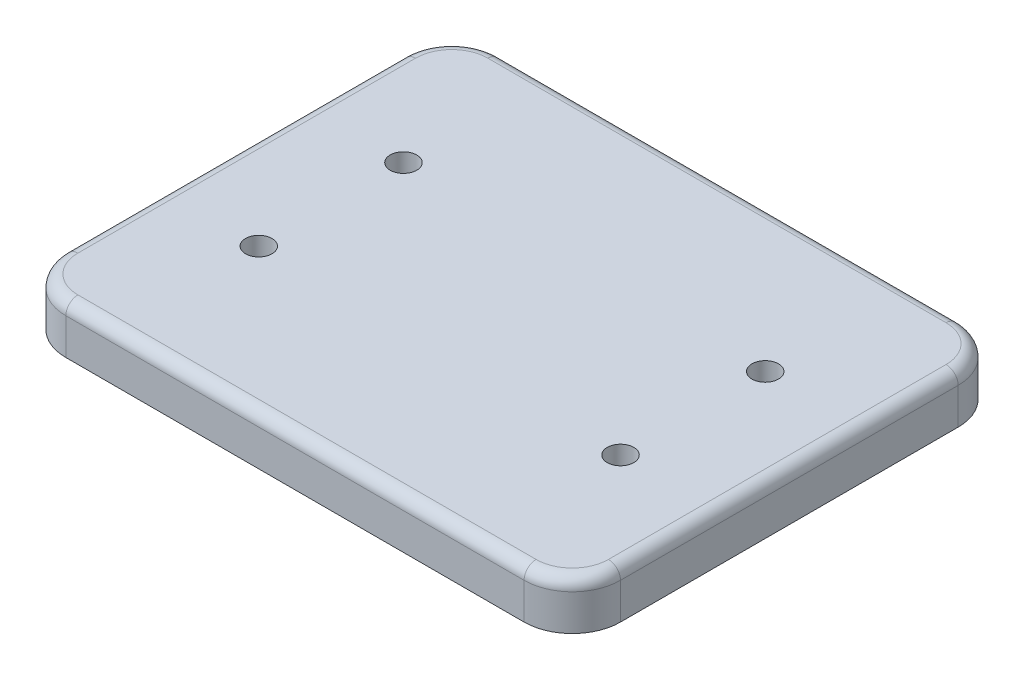
SolidWorks part; units mm, degrees
material "Oak"
ref_plane "Front Plane" through (0, 0, 0) normal (0, 0, 1) x (1, 0, 0)
ref_plane "Top Plane" through (0, 0, 0) normal (0, 1, 0) x (1, 0, 0)
ref_plane "Right Plane" through (0, 0, 0) normal (1, 0, 0) x (0, 0, -1)
sketch "Sketch1" plane through (0, 0, 0) normal (0, 1, 0) x (1, 0, 0)
  line L1 (-115, -90) -> (115, -90)
  line L2 (-115, -90) -> (-115, 90)
  line L3 (-115, 90) -> (115, 90)
  line L4 (115, -90) -> (115, 90)
  line L5 (-115, -90) -> (115, 90) construction
  line L6 (-115, 90) -> (115, -90) construction
  point P0 (0, 0)
  dimension "D1" = 230
  dimension "D2" = 180
extrude "Base" add sketch "Sketch1" along normal blind 20
fillet "R20 Fillets" radius 20 4 edges at (-115, 10, 90) (-115, 10, -90) (115, 10, -90) (115, 10, 90)
fillet "R5 Fillets" radius 5 8 edges at (-109.1421, 20, 84.1421) (-115, 20, 0) (-109.1421, 20, -84.1421) (0, 20, -90) (109.1421, 20, -84.1421) (115, 20, 0) (109.1421, 20, 84.1421) (0, 20, 90)
hole_wizard "Bolt Holes" positions "Sketch15" profile "Sketch10" legacy end condition through all
sketch "Sketch15" plane through (0, 0, 0) normal (0, -1, 0) x (-1, 0, 0)
  line L0 (0, 0) -> (0, 87.5586) construction
  line L2 (0, 0) -> (-115, 0) construction
  line L3 (-115, -70) -> (-115, 70) construction
  point P0 (-75, 30)
  point P2 (-75, -30)
  point P4 (75, -30)
  point P6 (75, 30)
  dimension "D1" = 60
  dimension "D2" = 60
  dimension "D3" = 150
  dimension "D4" = 150
sketch "Sketch10" plane through (75, 0, -30) normal (1, 0, 0) x (0, 0, -1)
  line L0 (0, 0) -> (0, 23.3047)
  line L1 (0, 23.3047) -> (5.5, 20)
  line L2 (5.5, 20) -> (5.5, 11)
  line L3 (5.5, 11) -> (9, 11)
  line L4 (9, 0) -> (0, 0)
  line L5 (0, -11.3109) -> (0, 121.1557) construction
  line L6 (0, 23.3047) -> (-5.5, 20) construction
  line L7 (9, 11) -> (9, 0)
  dimension "Depth" = 20
  dimension "Drill Angle" = 118
  dimension "Diameter" = 11
  dimension "C-Bore Diameter" = 18
  dimension "C-Bore Depth" = 11
